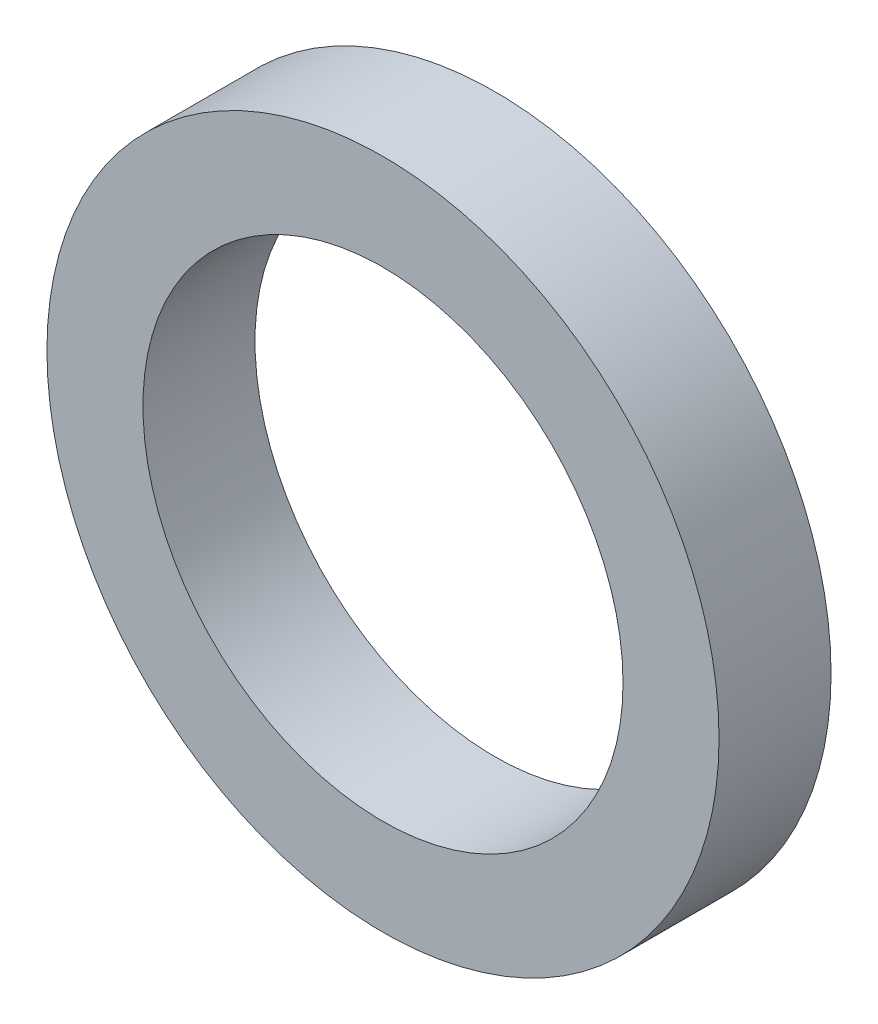
SolidWorks part; units mm, degrees
ref_plane "Front Plane" through (0, 0, 0) normal (0, 0, 1) x (1, 0, 0)
ref_plane "Top Plane" through (0, 0, 0) normal (0, 1, 0) x (1, 0, 0)
ref_plane "Right Plane" through (0, 0, 0) normal (1, 0, 0) x (0, 0, -1)
sketch "Sketch1" plane through (0, 0, 0) normal (0, 0, 1) x (1, 0, 0)
  circle A0 centre (0, 0) radius 21
  circle A1 centre (0, 0) radius 15
  dimension "D1" = 42
  dimension "D2" = 30
extrude "Extrude1" add sketch "Sketch1" along normal blind 7
